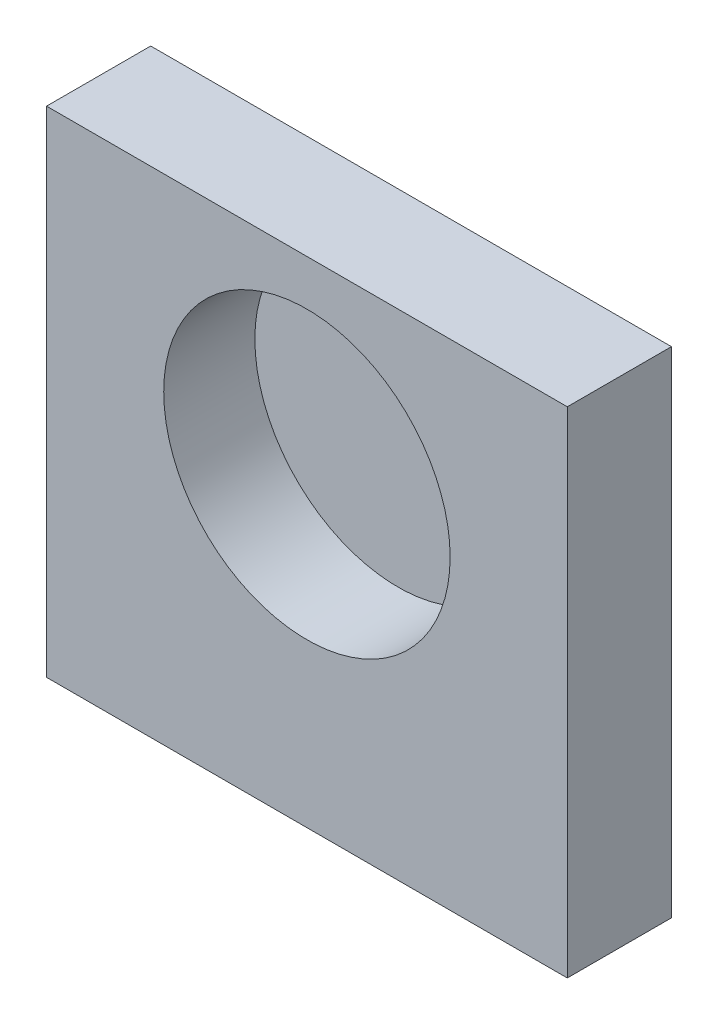
SolidWorks part; units mm, degrees
material "Liga 6061"
ref_plane "Plano frontal" through (0, 0, 0) normal (0, 0, 1) x (1, 0, 0)
ref_plane "Plano superior" through (0, 0, 0) normal (0, 1, 0) x (1, 0, 0)
ref_plane "Plano direito" through (0, 0, 0) normal (1, 0, 0) x (0, 0, -1)
sketch "Esboço1" plane through (0, 0, 0) normal (0, 0, 1) x (1, 0, 0)
  line L1 (20, -19) -> (-20, -19)
  line L2 (20, -19) -> (20, 19)
  line L3 (20, 19) -> (-20, 19)
  line L4 (-20, -19) -> (-20, 19)
  line L5 (20, -19) -> (-20, 19) construction
  line L6 (20, 19) -> (-20, -19) construction
  point P0 (0, 0)
  dimension "D1" = 38
  dimension "D2" = 40
extrude "Ressalto-extrusão1" add sketch "Esboço1" along normal blind 8
sketch "Esboço2" plane through (0, 0, 8) normal (0, 0, 1) x (1, 0, 0)
  line L0 (0, 21.191) -> (0, -23.0958) construction
  line L1 (-20, -19) -> (20, -19) construction
  circle A0 centre (0, 4.5) radius 11
  dimension "D1" = 22
  dimension "D2" = 23.5
extrude "Corte-extrusão1" cut sketch "Esboço2" against normal blind 7
hole_wizard "Furo roscado para conduíte de M3x0.51" positions "Esboço4" profile "Esboço5" tap size "M3x0.5" standard "Helicoil® Metric"
sketch "Esboço4" plane through (0, -19, 0) normal (0, -1, 0) x (-1, 0, 0)
  line L0 (-20, -8) -> (-20, 0) construction
  line L1 (20, 0) -> (-20, 0) construction
  line L2 (20, -8) -> (20, 0) construction
  point P0 (-12, -4)
  point P2 (12, -4)
  dimension "D1" = 8
  dimension "D2" = 4
  dimension "D3" = 8
  dimension "D4" = 4
sketch "Esboço5" plane through (12, -19, 4) normal (1, 0, 0) x (0, 0, -1)
  line L0 (0, 0) -> (0, 10.9464)
  line L1 (0, 10.9464) -> (1.575, 10)
  line L2 (1.575, 10) -> (1.575, 0.308)
  line L3 (1.575, 0.308) -> (1.883, 0)
  line L5 (1.883, 0) -> (0, 0)
  line L6 (-1.575, 0.308) -> (-1.883, 0) construction
  line L10 (0, 10.9464) -> (-1.575, 10) construction
  line L11 (0, -6.35) -> (0, 107.95) construction
  dimension "Tap Drill Dia." = 3.15
  dimension "Tap Drill Depth" = 10
  dimension "Near C'Sink Dia." = 3.766
  dimension "Near C'Sink Angle" = 90
  dimension "Drill Angle" = 118
cosmetic thread "Rosca de furo1" parameters "D1"=3.5, "D2"=3.716
cosmetic thread "Rosca de furo2" parameters "D1"=3.5, "D2"=3.716
